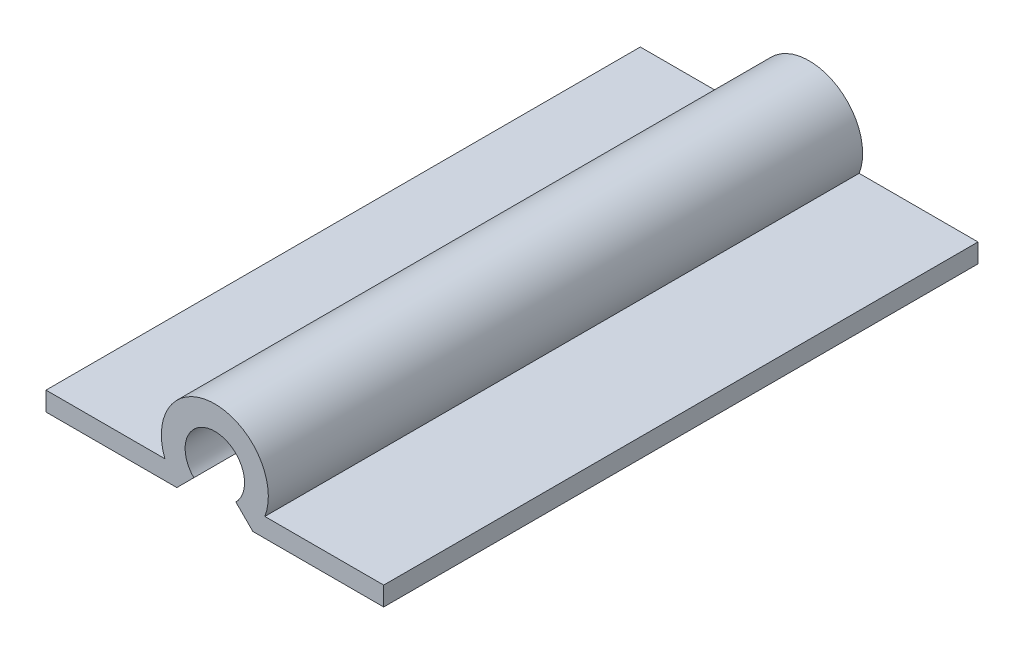
SolidWorks part; units mm, degrees
ref_plane "Front Plane" through (0, 0, 0) normal (0, 0, 1) x (1, 0, 0)
ref_plane "Top Plane" through (0, 0, 0) normal (0, 1, 0) x (1, 0, 0)
ref_plane "Right Plane" through (0, 0, 0) normal (1, 0, 0) x (0, 0, -1)
sketch "Sketch1" plane through (0, 0, 0) normal (0, 0, 1) x (1, 0, 0)
  line L0 (-2.6708, -1.016) -> (-9.0208, -1.016)
  line L1 (2.6708, -1.016) -> (9.0208, -1.016)
  line L2 (-9.0208, -2.032) -> (-2.032, -2.032)
  line L3 (2.032, -2.032) -> (9.0208, -2.032)
  line L4 (2.032, -2.032) -> (1.1225, -1.1225)
  line L5 (-2.032, -2.032) -> (-1.1225, -1.1225)
  line L6 (-9.0208, -1.016) -> (-9.0208, -2.032)
  line L7 (9.0208, -1.016) -> (9.0208, -2.032)
  arc A0 (1.1225, -1.1225) -> (-1.1225, -1.1225) centre (0, 0) ccw
  arc A1 (2.6708, -1.016) -> (-2.6708, -1.016) centre (0, 0) ccw
  circle A2 centre (0, 0) radius 2.8575 construction
  circle A3 centre (0, 0) radius 1.5875 construction
  point P4 (-5.5264, -2.032)
  dimension "D1" = 3.175
  dimension "D3" = 6.35
  dimension "D4" = 1.016
  dimension "D5" = 1.016
  dimension "D6" = 135
  dimension "D7" = 135
  dimension "D2" = 1.27
extrude "Boss-Extrude1" add sketch "Sketch1" along normal blind 31.75 contours L0 L6 L2 L5 A0 L4 L3 L7 L1 A1
